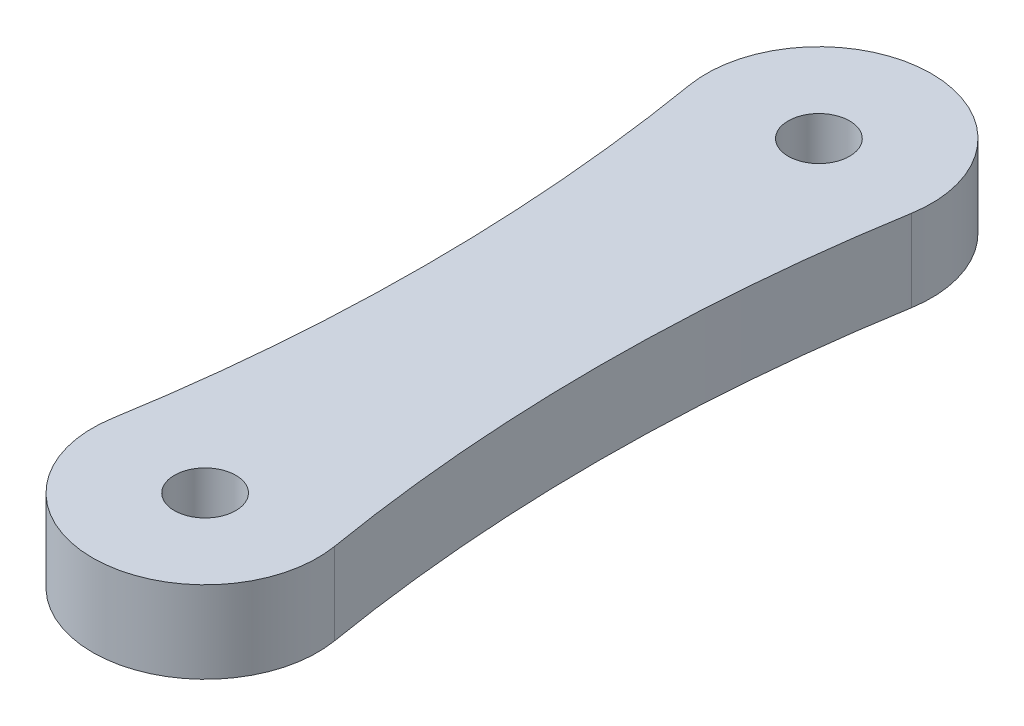
SolidWorks part; units mm, degrees
ref_plane "Front Plane" through (0, 0, 0) normal (0, 0, 1) x (1, 0, 0)
ref_plane "Top Plane" through (0, 0, 0) normal (0, 1, 0) x (1, 0, 0)
ref_plane "Right Plane" through (0, 0, 0) normal (1, 0, 0) x (0, 0, -1)
sketch "Sketch1" plane through (0, 0, 0) normal (0, 1, 0) x (1, 0, 0)
  line L0 (0, 0) -> (0, 30) construction
  line L3 (-4.25, 15) -> (4.25, 15) construction
  circle A2 centre (0, 0) radius 1.5
  circle A3 centre (0, 30) radius 1.5
  arc A8 (-5.4241, 0.9103) -> (5.4241, 0.9103) centre (0, 0) ccw
  arc A9 (5.4241, 29.0897) -> (-5.4241, 29.0897) centre (0, 30) ccw
  arc A10 (-5.4241, 29.0897) -> (-5.4241, 0.9103) centre (-89.375, 15) cw
  arc A11 (5.4241, 29.0897) -> (5.4241, 0.9103) centre (89.375, 15) ccw
  point P3 (0, 15)
  point P16 (-4.25, 15)
  point P19 (4.25, 15)
  point P23 (0, 15)
  dimension "D1" = 3
  dimension "D2" = 30
  dimension "D3" = 4
  dimension "D4" = 8.5
extrude "Boss-Extrude1" add sketch "Sketch1" along normal blind 4
